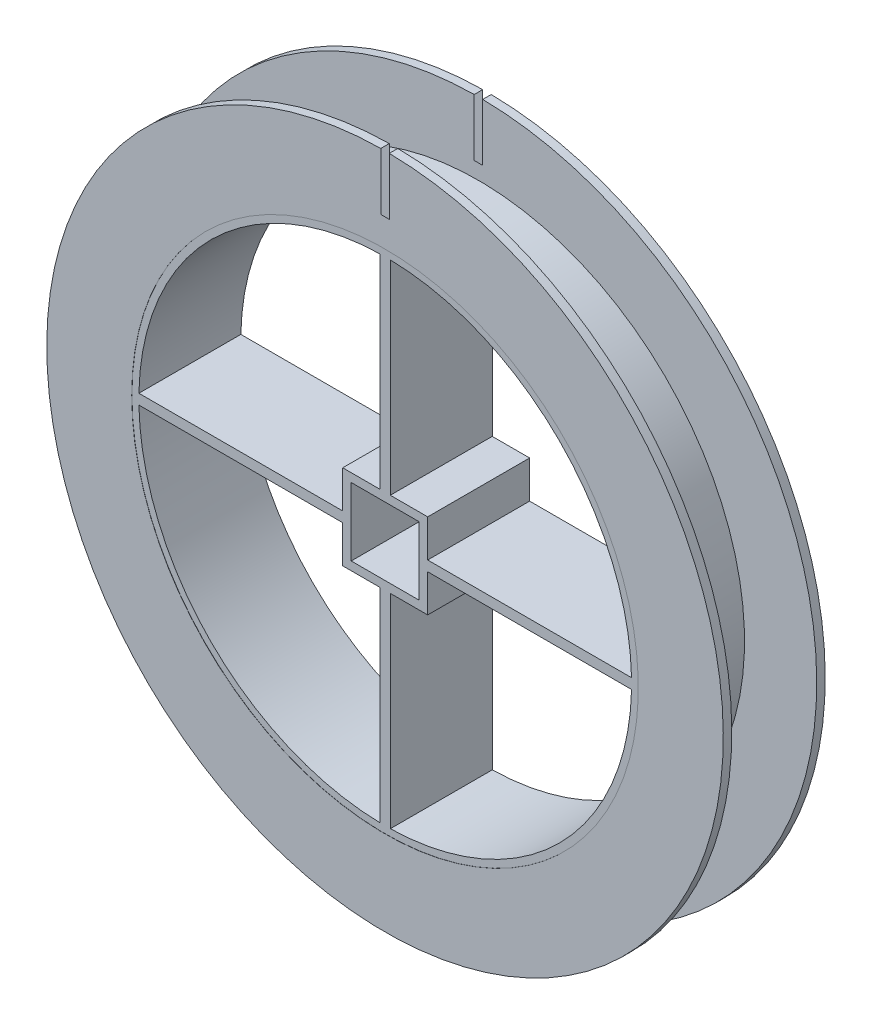
SolidWorks part; units mm, degrees
ref_plane "前视基准面" through (0, 0, 0) normal (0, 0, 1) x (1, 0, 0)
ref_plane "上视基准面" through (0, 0, 0) normal (0, 1, 0) x (1, 0, 0)
ref_plane "右视基准面" through (0, 0, 0) normal (1, 0, 0) x (0, 0, -1)
sketch "草图1" plane through (0, 0, 0) normal (0, 0, 1) x (1, 0, 0)
  circle A0 centre (0, 0) radius 30
  dimension "D1" = 60
sketch "草图4" plane through (0, 0, 0) normal (1, 0, 0) x (0, 0, -1)
  line L0 (-6.0215, 39.8148) -> (-5.0215, 39.8148)
  line L1 (-5.0215, 39.8148) -> (-5.0215, 31.3148)
  line L2 (-5.0215, 31.3148) -> (4.9785, 31.3148)
  line L3 (4.9785, 31.3148) -> (4.9785, 39.8148)
  line L4 (4.9785, 39.8148) -> (5.9785, 39.8148)
  line L5 (5.9785, 39.8148) -> (5.9785, 29.8148)
  line L6 (5.9785, 29.8148) -> (-6.0215, 29.8148)
  line L7 (-6.0215, 29.8148) -> (-6.0215, 39.8148)
  line L8 (-13.1815, 0) -> (18.5748, 0) construction
  dimension "D1" = 12
  dimension "D2" = 10
  dimension "D3" = 1
  dimension "D4" = 10
  dimension "D5" = 1.5
  dimension "D6" = 10
surface "曲面-旋转1" sketch "草图4" parameters "D1"=360
extrude "凸台-拉伸2" add sketch "草图1" along normal mid plane 12
sketch "草图6" plane through (0, 0, 6) normal (0, 0, 1) x (1, 0, 0)
  line L0 (-0.6, 28.9938) -> (-0.6, 5)
  line L1 (-28.9938, -0.6) -> (-5, -0.6)
  line L2 (0.6, 28.9938) -> (0.6, 5)
  line L3 (-28.9938, 0.6) -> (-5, 0.6)
  line L4 (0.6, 5) -> (5, 5)
  line L6 (5, -0.6) -> (28.9938, -0.6)
  line L7 (5, 0.6) -> (28.9938, 0.6)
  line L10 (-0.6, -5) -> (-0.6, -28.9938)
  line L11 (0.6, -5) -> (0.6, -28.9938)
  line L14 (-4, 4) -> (4, 4)
  line L15 (-5, 5) -> (-0.6, 5)
  line L16 (-5, 5) -> (-5, 0.6)
  line L17 (-5, -5) -> (-0.6, -5)
  line L18 (5, 5) -> (5, 0.6)
  line L19 (-4, 4) -> (-4, -4)
  line L20 (-4, -4) -> (4, -4)
  line L21 (5, -0.6) -> (5, -5)
  line L22 (-5, -0.6) -> (-5, -5)
  line L23 (0.6, -5) -> (5, -5)
  line L24 (4, 4) -> (4, -4)
  line L25 (-4, 4) -> (4, -4) construction
  line L26 (-4, -4) -> (4, 4) construction
  arc A1 (-0.6, 28.9938) -> (-28.9938, 0.6) centre (0, 0) ccw
  arc A4 (-28.9938, -0.6) -> (-0.6, -28.9938) centre (0, 0) ccw
  arc A5 (28.9938, 0.6) -> (0.6, 28.9938) centre (0, 0) ccw
  arc A9 (0.6, -28.9938) -> (28.9938, -0.6) centre (0, 0) ccw
  dimension "D1" = 58
  dimension "D2" = 8
  dimension "D3" = 8
  dimension "D4" = 0.6
  dimension "D5" = 0.6
  dimension "D6" = 0.6
  dimension "D7" = 0.6
  dimension "D9" = 10
  dimension "D10" = 10
extrude "切除-拉伸2" cut sketch "草图6" against normal through all
sketch "草图16" plane through (0, 0, 6.0215) normal (0, 0, 1) x (1, 0, 0)
  line L1 (-0.5, 46.5448) -> (0.5, 46.5448)
  line L2 (-0.5, 46.5448) -> (-0.5, 33.0848)
  line L3 (-0.5, 33.0848) -> (0.5, 33.0848)
  line L4 (0.5, 46.5448) -> (0.5, 33.0848)
  circle A1 centre (0, 0) radius 39.8148 construction
  point P0 (0, 39.8148)
  dimension "D1" = 1
surface "曲面-剪裁2"
